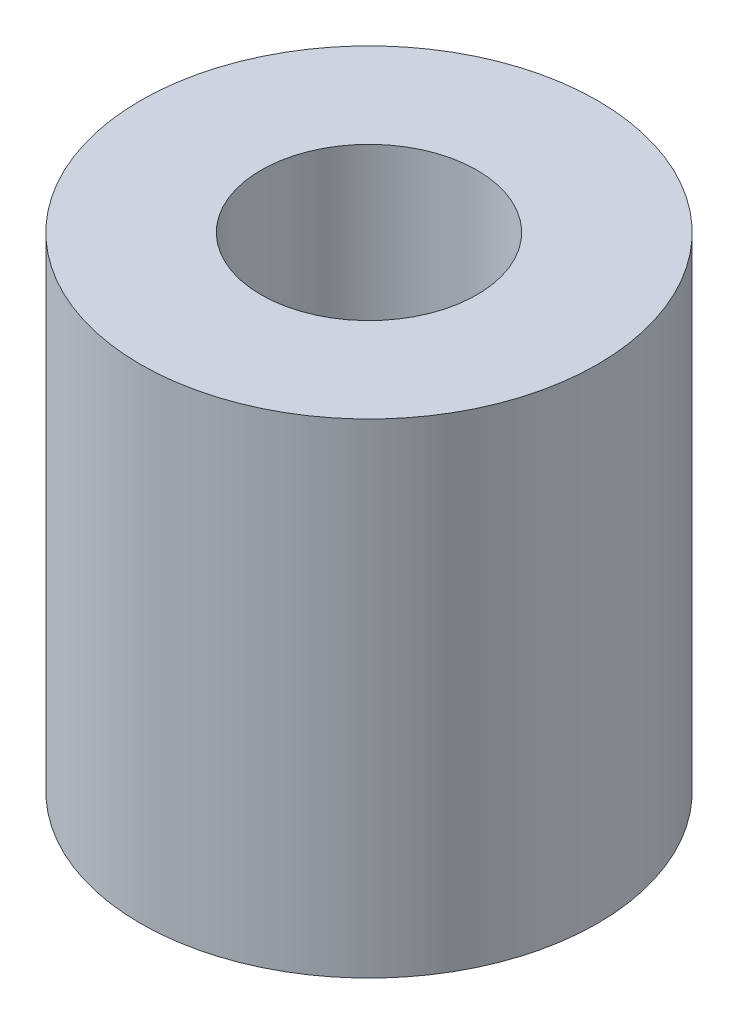
SolidWorks part; units mm, degrees
ref_plane "Front Plane" through (0, 0, 0) normal (0, 0, 1) x (1, 0, 0)
ref_plane "Top Plane" through (0, 0, 0) normal (0, 1, 0) x (1, 0, 0)
ref_plane "Right Plane" through (0, 0, 0) normal (1, 0, 0) x (0, 0, -1)
sketch "Sketch1" plane through (0, 0, 0) normal (0, 1, 0) x (1, 0, 0)
  circle A0 centre (0, 0) radius 4.55
  circle A1 centre (0, 0) radius 2.15
extrude "Boss-Extrude1" add sketch "Sketch1" along normal blind 9.64
